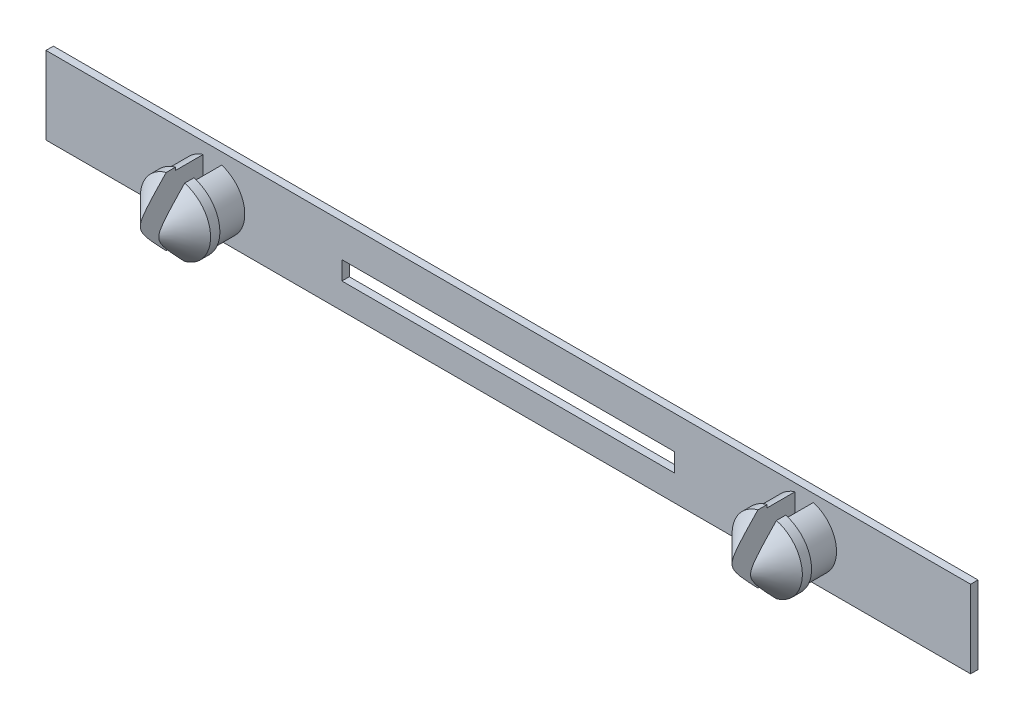
SolidWorks part; units mm, degrees
ref_plane "Přední rovina" through (0, 0, 0) normal (0, 0, 1) x (1, 0, 0)
ref_plane "Horní rovina" through (0, 0, 0) normal (0, 1, 0) x (1, 0, 0)
ref_plane "Pravá rovina" through (0, 0, 0) normal (1, 0, 0) x (0, 0, -1)
sketch "Skica2" plane through (0, 0, 0) normal (0, 0, 1) x (1, 0, 0)
  line L1 (-25, 2.1) -> (25, 2.1)
  line L2 (-25, 2.1) -> (-25, -2.1)
  line L3 (-25, -2.1) -> (25, -2.1)
  line L4 (25, 2.1) -> (25, -2.1)
  line L5 (-25, 2.1) -> (25, -2.1) construction
  line L6 (-25, -2.1) -> (25, 2.1) construction
  line L7 (9, 0.3) -> (-9, 0.3)
  line L8 (9, 0.3) -> (9, -0.7)
  line L9 (9, -0.7) -> (-9, -0.7)
  line L10 (-9, 0.3) -> (-9, -0.7)
  line L11 (9, 0.3) -> (-9, -0.7) construction
  line L12 (9, -0.7) -> (-9, 0.3) construction
  point P0 (0, 0)
  point P5 (0, -0.2)
  dimension "D1" = 4.2
  dimension "D2" = 50
  dimension "D3" = 1
  dimension "D4" = 18
  dimension "D5" = 16
  dimension "D6" = 16
extrude "Přidat vysunutím2" add sketch "Skica2" along normal blind 0.4
sketch "Skica3" plane through (0, 0, 0.4) normal (0, 0, 1) x (1, 0, 0)
  line L0 (-25, 2.1) -> (-25, -2.1) construction
  line L1 (25, -2.1) -> (25, 2.1) construction
  line L2 (25, 2.1) -> (-25, 2.1) construction
  line L3 (-25, -2.1) -> (25, -2.1) construction
  circle A0 centre (-16, -0.2) radius 1.75
  circle A1 centre (16, 0) radius 1.75
  dimension "D1" = 3.5
  dimension "D3" = 3.5
  dimension "D2" = 9
  dimension "D4" = 9
  dimension "D5" = 2.3
  dimension "D6" = 1.9
extrude "Přidat vysunutím3" add sketch "Skica3" along normal blind 1.5
sketch "Skica5" plane through (0, 0, 1.9) normal (0, 0, 1) x (1, 0, 0)
  circle A0 centre (-16, -0.2) radius 1.9
  circle A1 centre (16, 0) radius 1.9
  dimension "D1" = 3.8
  dimension "D2" = 3.8
extrude "Přidat vysunutím5" add sketch "Skica5" along normal blind 2
chamfer "Zkosení2" distance 1.5 angle 45 2 edges at (17.9, 0, 3.9) (-14.1, -0.2, 3.9)
sketch "Skica7" plane through (0, 0, 3.9) normal (0, 0, 1) x (1, 0, 0)
  line L1 (-15.5, 2.3) -> (-16.5, 2.3)
  line L2 (-15.5, 2.3) -> (-15.5, -2.7)
  line L3 (-15.5, -2.7) -> (-16.5, -2.7)
  line L4 (-16.5, 2.3) -> (-16.5, -2.7)
  line L5 (-15.5, 2.3) -> (-16.5, -2.7) construction
  line L6 (-15.5, -2.7) -> (-16.5, 2.3) construction
  line L7 (15.5, 2.5) -> (16.5, 2.5)
  line L8 (15.5, 2.5) -> (15.5, -2.5)
  line L9 (15.5, -2.5) -> (16.5, -2.5)
  line L10 (16.5, 2.5) -> (16.5, -2.5)
  line L11 (15.5, 2.5) -> (16.5, -2.5) construction
  line L12 (15.5, -2.5) -> (16.5, 2.5) construction
  point P0 (-16, -0.2)
  point P5 (16, 0)
  dimension "D1" = 5
  dimension "D2" = 1
  dimension "D3" = 5
  dimension "D4" = 1
extrude "Odebrat vysunutím1" cut sketch "Skica7" against normal blind 3.5
equation "\"1.5.000mm\"=10"
